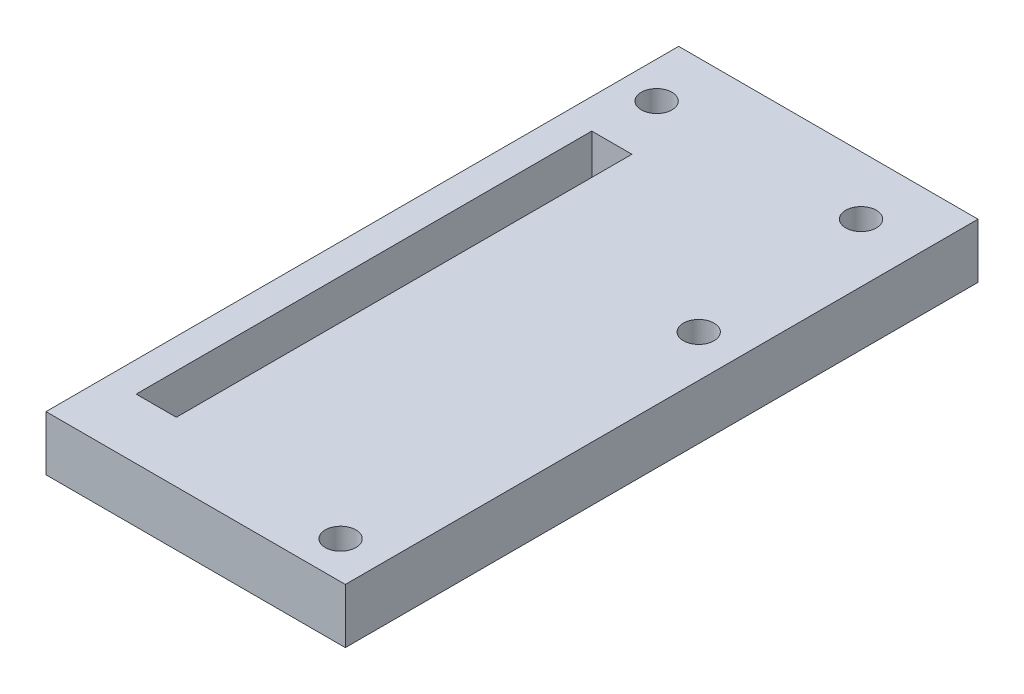
SolidWorks part; units mm, degrees
ref_plane "Front Plane" through (0, 0, 0) normal (0, 0, 1) x (1, 0, 0)
ref_plane "Top Plane" through (0, 0, 0) normal (0, 1, 0) x (1, 0, 0)
ref_plane "Right Plane" through (0, 0, 0) normal (1, 0, 0) x (0, 0, -1)
sketch "Sketch1" plane through (0, 0, 0) normal (0, 1, 0) x (1, 0, 0)
  line L1 (25, 43.325) -> (-25, 43.325)
  line L2 (25, 43.325) -> (25, -43.325)
  line L3 (25, -43.325) -> (-25, -43.325)
  line L4 (-25, 43.325) -> (-25, -43.325)
  line L5 (25, 43.325) -> (-25, -43.325) construction
  line L6 (25, -43.325) -> (-25, 43.325) construction
  point P0 (0, 0)
  dimension "D1" = 86.65
  dimension "D2" = 50
extrude "Boss-Extrude1" add sketch "Sketch1" along normal blind 7.5
sketch "Sketch7" plane through (0, 7.5, 0) normal (0, 1, 0) x (1, 0, 0)
  line L0 (-5.4, 27.325) -> (-5.4, -35.075)
  line L1 (-5.4, -35.075) -> (-10.9, -35.075)
  line L2 (-10.9, -35.075) -> (-10.9, 27.325)
  line L3 (-10.9, 27.325) -> (-5.4, 27.325)
  line L6 (25, 43.325) -> (-25, 43.325) construction
  line L7 (25, -43.325) -> (25, 43.325) construction
  dimension "D1" = 30.4
  dimension "D2" = 16
  dimension "D3" = 5.5
  dimension "D4" = 62.4
extrude "Cut-Extrude5" cut sketch "Sketch7" against normal blind 5.95 contours L0 L1 L2 L3
sketch "Sketch11" plane through (0, 7.5, 0) normal (0, 1, 0) x (1, 0, 0)
  line L0 (25, -43.325) -> (25, 43.325) construction
  line L1 (25, 43.325) -> (-25, 43.325) construction
  circle A0 centre (17.982, 35.325) radius 2.1
  circle A1 centre (-10.018, 35.325) radius 2.1
  dimension "D3" = 4.2
  dimension "D4" = 4.2
  dimension "D1" = 7.018
  dimension "D2" = 35.018
  dimension "D5" = 8
  dimension "D6" = 8
extrude "Cut-Extrude8" cut sketch "Sketch11" against normal through all
sketch "Sketch12" plane through (0, 7.5, 0) normal (0, 1, 0) x (1, 0, 0)
  line L0 (-5.4, 27.325) -> (-5.4, -35.075) construction
  line L1 (-5.4, 27.325) -> (-5.4, -35.075) construction
  line L2 (25, 43.325) -> (-25, 43.325) construction
  circle A0 centre (20.25, 10.821) radius 2.1
  circle A1 centre (20.25, -38.229) radius 2.1
  dimension "D3" = 49.05
  dimension "D5" = 4.2
  dimension "D6" = 4.2
  dimension "D1" = 25.65
  dimension "D2" = 25.65
  dimension "D4" = 32.504
extrude "Cut-Extrude10" cut sketch "Sketch12" against normal through all
sketch "Sketch13" plane through (25, 0, 0) normal (1, 0, 0) x (0, 0, -1)
  line L1 (-43.325, 7.5) -> (43.325, 7.5)
  line L2 (-43.325, 7.5) -> (-43.325, 0)
  line L3 (-43.325, 0) -> (43.325, 0)
  line L4 (43.325, 7.5) -> (43.325, 0)
extrude "Boss-Extrude2" add sketch "Sketch13" along normal blind 1
sketch "Sketch14" plane through (-25, 0, 0) normal (-1, 0, 0) x (0, 0, 1)
  line L1 (-43.325, 7.5) -> (43.325, 7.5)
  line L2 (-43.325, 7.5) -> (-43.325, 0)
  line L3 (-43.325, 0) -> (43.325, 0)
  line L4 (43.325, 7.5) -> (43.325, 0)
extrude "Cut-Extrude11" cut sketch "Sketch14" against normal blind 10
